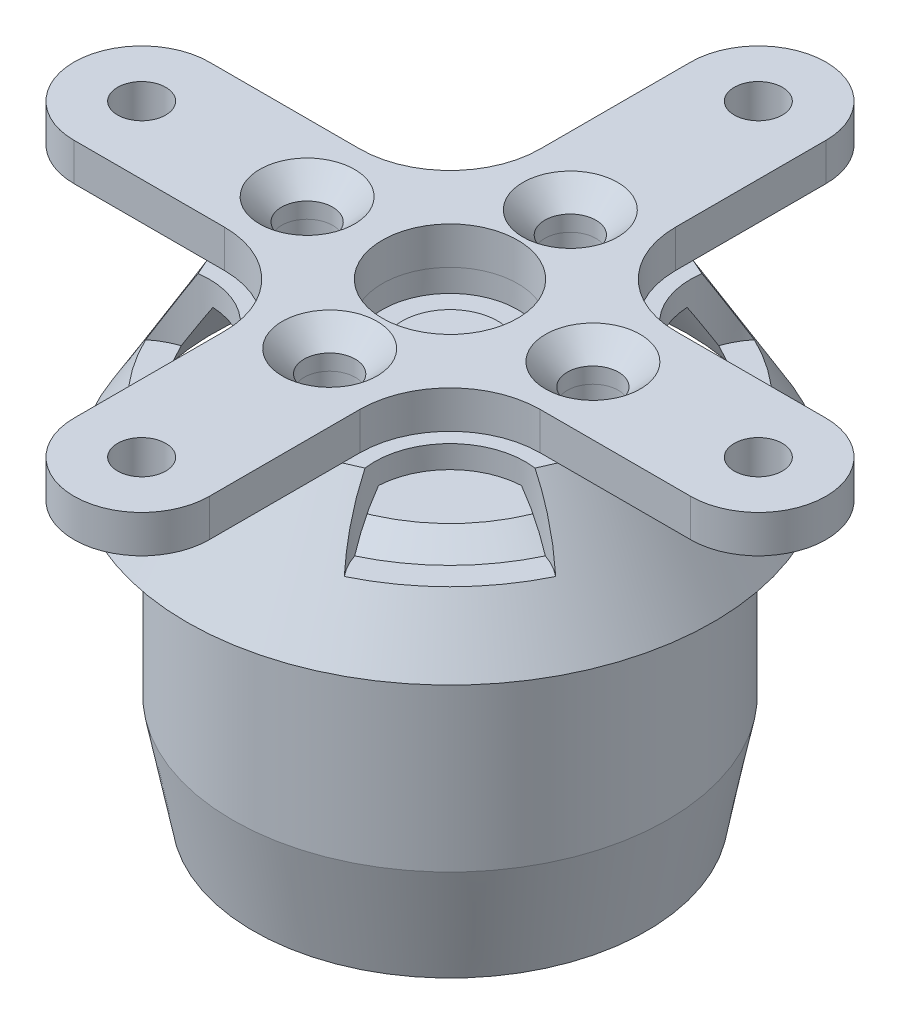
SolidWorks part; units mm, degrees
ref_plane "Plano frontal" through (0, 0, 0) normal (0, 0, 1) x (1, 0, 0)
ref_plane "Plano superior" through (0, 0, 0) normal (0, 1, 0) x (1, 0, 0)
ref_plane "Plano direito" through (0, 0, 0) normal (1, 0, 0) x (0, 0, -1)
sketch "Sketch2" plane through (0, 0, 0) normal (0, 1, 0) x (1, 0, 0)
  line L0 (0, 20.5) -> (0, 0) construction
  line L1 (4.5, 20.5) -> (4.5, 10.5)
  line L2 (-4.5, 20.5) -> (-4.5, 10.5)
  line L3 (4.5, 4.5) -> (-4.5, 4.5) construction
  line L4 (20.5, 4.5) -> (10.5, 4.5)
  line L5 (20.5, -4.5) -> (10.5, -4.5)
  line L6 (4.5, -20.5) -> (4.5, -10.5)
  line L7 (-4.5, -20.5) -> (-4.5, -10.5)
  line L8 (-20.5, -4.5) -> (-10.5, -4.5)
  line L9 (-20.5, 4.5) -> (-10.5, 4.5)
  circle A0 centre (0, 0) radius 25 construction
  circle A1 centre (0, 0) radius 4.5
  circle A2 centre (0, 20.5) radius 1.6
  arc A3 (4.5, 20.5) -> (-4.5, 20.5) centre (0, 20.5) ccw
  circle A4 centre (20.5, 0) radius 1.6
  arc A5 (20.5, -4.5) -> (20.5, 4.5) centre (20.5, 0) ccw
  circle A6 centre (0, -20.5) radius 1.6
  arc A7 (-4.5, -20.5) -> (4.5, -20.5) centre (0, -20.5) ccw
  circle A8 centre (-20.5, 0) radius 1.6
  arc A9 (-20.5, 4.5) -> (-20.5, -4.5) centre (-20.5, 0) ccw
  arc A10 (-4.5, -10.5) -> (-10.5, -4.5) centre (-10.5, -10.5) ccw
  arc A11 (10.5, -4.5) -> (4.5, -10.5) centre (10.5, -10.5) ccw
  arc A12 (4.5, 10.5) -> (10.5, 4.5) centre (10.5, 10.5) ccw
  arc A13 (-4.5, 10.5) -> (-10.5, 4.5) centre (-10.5, 10.5) cw
  point P31 (0, 0)
  dimension "D1" = 50
  dimension "D2" = 9
  dimension "D3" = 3.2
  dimension "D6" = 6
  dimension "D4" = 20.5
  dimension "D5" = 4
extrude "Boss-Extrude1" add sketch "Sketch2" along normal blind 2.5
sketch "Sketch3" plane through (0, 0, 0) normal (1, 0, 0) x (0, 0, -1)
  line L0 (0, 0) -> (0, -54.7742) construction
  line L1 (-17.5, -8.5) -> (-12.5, 0)
  line L3 (-20.5, 0) -> (-10.5, 0) construction
  line L4 (-17.5, -8.5) -> (0, -8.5)
  line L5 (0, -8.5) -> (0, 0)
  line L6 (0, 0) -> (-12.5, 0)
revolve "Revolve1" add sketch "Sketch3" angle 360 about L0
sketch "Sketch4" plane through (0, 0, 0) normal (0, 1, 0) x (1, 0, 0)
  line L0 (0, -8) -> (0, 0) construction
  line L1 (0, 0) -> (0, 8) construction
  line L2 (-9.5, 0) -> (0, 0) construction
  line L3 (0, 0) -> (9.5, 0) construction
  circle A0 centre (0, 8) radius 1.5
  circle A1 centre (0, -8) radius 1.5
  circle A2 centre (9.5, 0) radius 1.5
  circle A3 centre (-9.5, 0) radius 1.5
  dimension "D3" = 3
  dimension "D1" = 16
  dimension "D2" = 19
extrude "Cut-Extrude1" cut sketch "Sketch4" along normal through all and the other way through all
sketch "Sketch5" plane through (0, 0, 0) normal (0, 1, 0) x (1, 0, 0)
  circle A0 centre (10.5, 10.5) radius 5
  arc A1 (4.5, 10.5) -> (10.5, 4.5) centre (10.5, 10.5) ccw construction
  circle A2 centre (10.5, -10.5) radius 5
  circle A3 centre (-10.5, -10.5) radius 5
  circle A4 centre (-10.5, 10.5) radius 5
  circle A5 centre (0, 0) radius 14.8492 construction
  point P14 (0, 0)
  dimension "D2" = 1
  dimension "D1" = 4
extrude "Cut-Extrude2" cut sketch "Sketch5" against normal blind 4.5
sketch "Sketch6" plane through (0, 0, 0) normal (1, 0, 0) x (0, 0, -1)
  line L0 (0, -8.5) -> (0, 0) construction
  line L1 (-17.5, -8.5) -> (17.5, -8.5) construction
  line L2 (-15.7597, -8.5) -> (-11.6421, -1.5)
  line L3 (-11.6421, -1.5) -> (0, -1.5)
  line L4 (0, -1.5) -> (0, -8.5)
  line L5 (0, -8.5) -> (-15.7597, -8.5)
  line L6 (-12.5, 0) -> (-17.5, -8.5) construction
  line L8 (-12.5, 0) -> (-17.5, -8.5) construction
  dimension "D1" = 1.5
  dimension "D2" = 1.5
revolve "Cut-Revolve1" cut sketch "Sketch6" angle 360 about L0
sketch "Sketch7" plane through (0, 0, 0) normal (0, 1, 0) x (1, 0, 0)
  circle A0 centre (0, 0) radius 4.5 construction
  circle A1 centre (0, 0) radius 4.5
extrude "Cut-Extrude3" cut sketch "Sketch7" against normal through all
hole_wizard "CSK for M3 Flat Head Machine Screw1" positions "Sketch9" profile "Sketch8" countersink size "M3" standard "ANSI Metric"
sketch "Sketch9" plane through (0, 2.5, 0) normal (0, 1, 0) x (1, 0, 0)
  point P0 (9.5, 0)
  point P3 (0, -8)
  point P6 (-9.5, 0)
  point P9 (0, 8)
sketch "Sketch8" plane through (9.5, 2.5, 0) normal (1, 0, 0) x (0, 0, 1)
  line L0 (0, 0) -> (0, 11)
  line L1 (0, 11) -> (1.7, 11)
  line L2 (1.7, 11) -> (1.7, 1.45)
  line L3 (1.7, 1.45) -> (3.15, 0)
  line L5 (3.15, 0) -> (0, 0)
  line L6 (-1.7, 1.45) -> (-3.15, 0) construction
  line L11 (0, -6.35) -> (0, 107.95) construction
  dimension "Thru Hole Dia." = 3.4
  dimension "Thru Hole Depth" = 11
  dimension "Near C'Sink Dia." = 6.3
  dimension "Near C'Sink Angle" = 90
sketch "Sketch10" plane through (0, 0, 0) normal (0, 0, 1) x (1, 0, 0)
  line L0 (3.1825, -1.5) -> (3.1825, -4.5)
  line L2 (3.1825, -4.5) -> (10, -4.5)
  line L3 (12.1043, -4.5) -> (5.7644, -4.5) construction
  line L4 (-4.5, -1.5) -> (4.5, -1.5) construction
  line L5 (0, -1.5) -> (0, -28.5)
  line L6 (17.5, -28.5) -> (-17.5, -28.5) construction
  line L7 (0, -28.5) -> (13.0709, -28.5)
  line L8 (13.0709, -28.5) -> (14.4546, -21.4163)
  line L9 (14.4546, -21.4163) -> (14.4546, -8.0682)
  line L10 (14.4546, -8.0682) -> (10, -4.5)
  line L11 (10, -4.5) -> (9.9569, -4.4625)
  line L12 (0, -1.5) -> (3.1825, -1.5)
  dimension "D1" = 3
revolve "Revolve2" add sketch "Sketch10" angle 360 about L5
sketch "Esboço1" plane through (0, -1.5, 0) normal (0, 1, 0) x (1, 0, 0)
  point P0 (0, 0)
